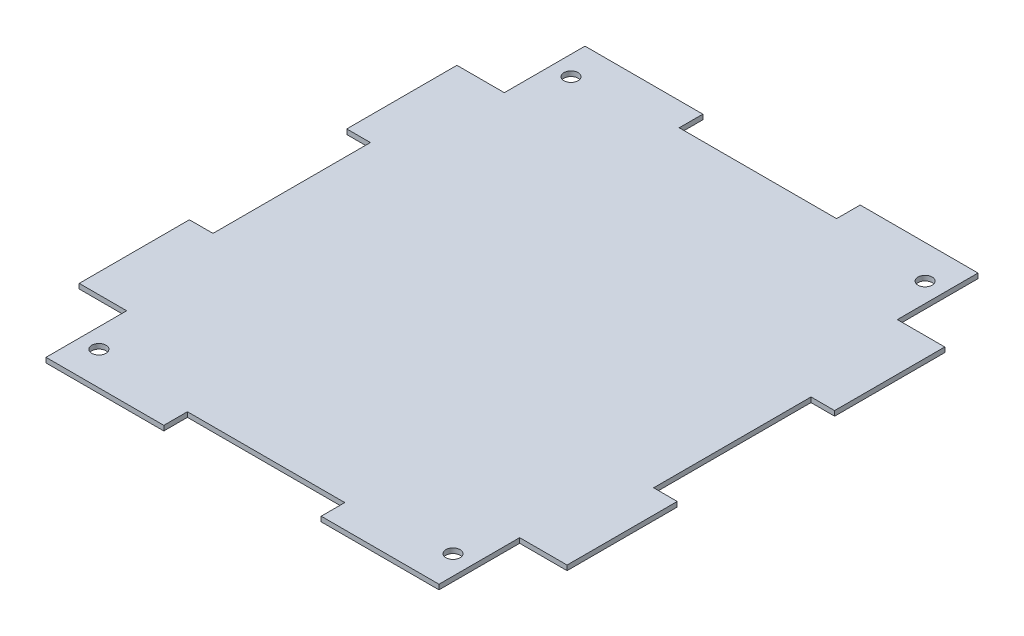
SolidWorks part; units mm, degrees
ref_plane "Front Plane" through (0, 0, 0) normal (0, 0, 1) x (1, 0, 0)
ref_plane "Top Plane" through (0, 0, 0) normal (0, 1, 0) x (1, 0, 0)
ref_plane "Right Plane" through (0, 0, 0) normal (1, 0, 0) x (0, 0, -1)
sketch "Sketch1" plane through (0, 0, 0) normal (0, 1, 0) x (1, 0, 0)
  line L0 (-25.4, 86.995) -> (-63.4314, 86.995)
  line L1 (-88.9, -101.6) -> (88.9, -101.6) construction
  line L2 (101.6, -88.9) -> (101.6, 88.9) construction
  line L3 (88.9, 101.6) -> (-88.9, 101.6) construction
  line L4 (-78.74, -60.96) -> (-63.4314, -60.96)
  line L5 (-63.4314, -60.96) -> (-63.4314, -86.995)
  line L6 (-63.4314, -86.995) -> (-25.4, -86.995)
  line L7 (63.4314, -86.995) -> (63.4314, -60.96)
  line L8 (63.4314, -60.96) -> (78.74, -60.96)
  line L9 (78.74, -60.96) -> (78.74, -25.4)
  line L10 (78.74, 60.96) -> (63.4314, 60.96)
  line L11 (63.4314, 60.96) -> (63.4314, 86.995)
  line L12 (63.4314, 86.995) -> (25.4, 86.995)
  line L13 (-63.4314, 86.995) -> (-63.4314, 60.96)
  line L14 (-63.4314, 60.96) -> (-78.74, 60.96)
  line L15 (-78.74, 60.96) -> (-78.74, 25.4)
  line L16 (-78.74, -25.4) -> (-78.74, -60.96)
  line L17 (-78.74, -25.4) -> (-71.12, -25.4)
  line L19 (-78.74, 25.4) -> (-71.12, 25.4)
  line L20 (-71.12, -25.4) -> (-71.12, 25.4)
  line L22 (-25.4, 86.995) -> (-25.4, 79.375)
  line L23 (-25.4, 79.375) -> (25.4, 79.375)
  line L24 (25.4, 86.995) -> (25.4, 79.375)
  line L25 (78.74, 25.4) -> (71.12, 25.4)
  line L27 (78.74, -25.4) -> (71.12, -25.4)
  line L28 (71.12, 25.4) -> (71.12, -25.4)
  line L30 (25.4, -86.995) -> (25.4, -79.375)
  line L31 (25.4, -79.375) -> (-25.4, -79.375)
  line L32 (-25.4, -86.995) -> (-25.4, -79.375)
  line L33 (78.74, 25.4) -> (78.74, 60.96)
  line L34 (25.4, -86.995) -> (63.4314, -86.995)
  line L35 (-101.6, 88.9) -> (-101.6, -88.9) construction
  arc A0 (88.9, -101.6) -> (101.6, -88.9) centre (88.9, -88.9) ccw construction
  arc A1 (-101.6, -88.9) -> (-88.9, -101.6) centre (-88.9, -88.9) ccw construction
  arc A2 (101.6, 88.9) -> (88.9, 101.6) centre (88.9, 88.9) ccw construction
  arc A3 (-101.6, 88.9) -> (-88.9, 101.6) centre (-88.9, 88.9) cw construction
  circle A4 centre (-57.15, 76.2) radius 2.286
  circle A5 centre (57.15, 76.2) radius 2.286
  circle A6 centre (57.15, -76.2) radius 2.286
  circle A7 centre (-57.15, -76.2) radius 2.286
  point P3 (0, 101.6)
  point P5 (101.6, 0)
  point P13 (101.6, 101.6)
  point P16 (-101.6, 101.6)
  point P38 (-71.12, 0)
  point P55 (0, -79.375)
  point P56 (0, 79.375)
  point P57 (71.12, 0)
  dimension "D2" = 12.7
  dimension "D11" = 4.572
  dimension "D8" = 44.45
  dimension "D1" = 203.2
  dimension "D3" = 203.2
  dimension "D4" = 22.86
  dimension "D5" = 15.3086
  dimension "D6" = 35.56
  dimension "D7" = 173.99
  dimension "D12" = 50.8
  dimension "D13" = 25.4
  dimension "D14" = 44.45
  dimension "D15" = 25.4
  dimension "D18" = 7.62
extrude "Main Body" add sketch "Sketch1" along normal blind 1.5875
